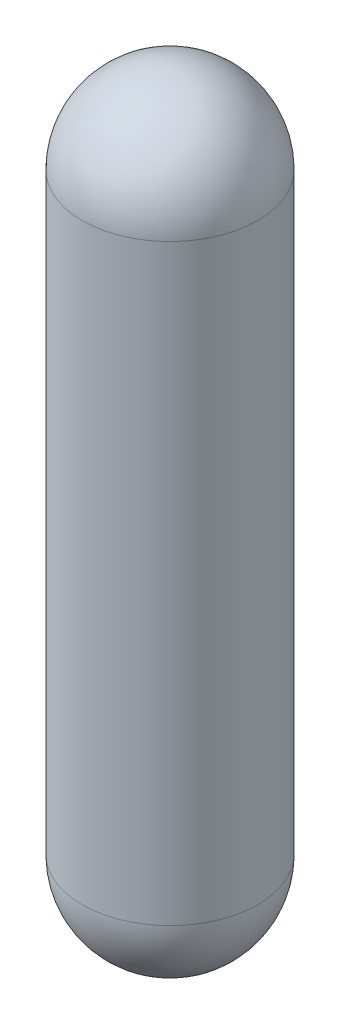
SolidWorks part; units mm, degrees
other "Markup1"
sketch "Sketch2" plane through (-160, -160, 160) normal (0, 0, 1) x (1, 0, 0)
material "Titanium"
ref_plane "Front Plane" through (0, 0, 0) normal (0, 0, 1) x (1, 0, 0)
ref_plane "Top Plane" through (0, 0, 0) normal (0, 1, 0) x (1, 0, 0)
ref_plane "Right Plane" through (0, 0, 0) normal (1, 0, 0) x (0, 0, -1)
sketch "Sketch1" plane through (0, 0, 0) normal (0, 0, 1) x (1, 0, 0)
  line L0 (0, 1768.86) -> (0, 1771.4)
  line L2 (0, 0) -> (0, 1542.8) construction
  line L5 (0, -226.06) -> (0, -228.6)
  line L6 (0, 738.4774) -> (228.6, 738.4774) construction
  line L7 (215.2638, 1542.8) -> (215.2638, 0)
  line L8 (215.2638, 1096.4433) -> (217.8038, 1096.4433) construction
  line L9 (228.6, 1542.8) -> (228.6, 0)
  line L10 (0, 1768.86) -> (0, 1542.8) construction
  line L11 (0, 0) -> (0, -226.06) construction
  arc A0 (0, -228.6) -> (228.6, 0) centre (0, 0) ccw
  arc A1 (228.6, 1542.8) -> (0, 1771.4) centre (0, 1542.8) ccw
  arc A2 (215.2638, 1542.8) -> (0, 1768.86) centre (-10.7961, 1543.0579) ccw
  arc A3 (215.2638, 0) -> (0, -226.06) centre (-10.7961, -0.2579) cw
  dimension "D4" = 228.6
  dimension "D5" = 1542.8
  dimension "D6" = 226.06
  dimension "D7" = 226.06
  dimension "D8" = 228.6
  dimension "D1" = 228.6
  dimension "D2" = 2000
  dimension "D3" = 2.54
  dimension "D9" = 228.6
revolve "Revolve1" add sketch "Sketch1" angle 360 about L2
